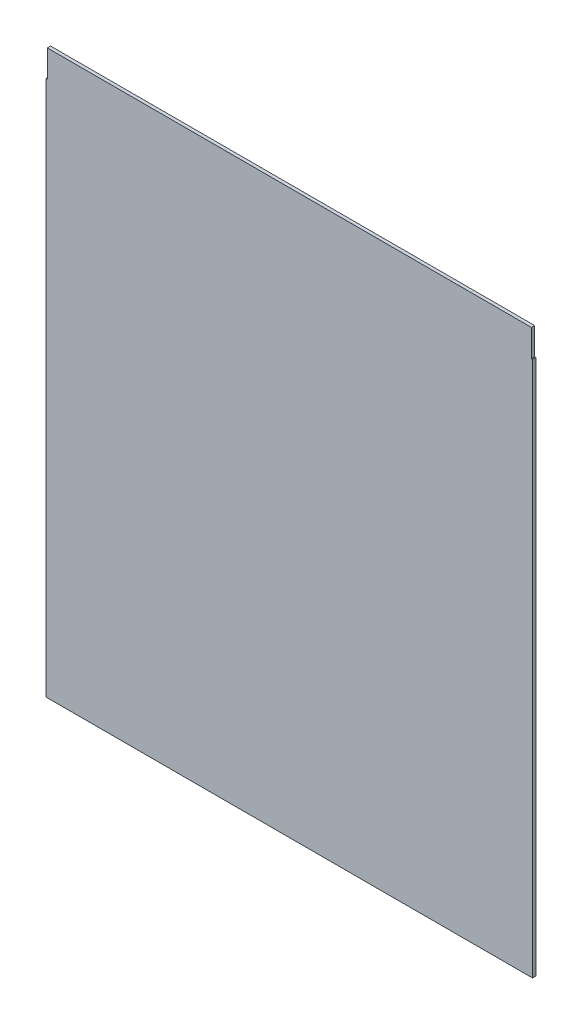
SolidWorks part; units mm, degrees
ref_plane "Alzado" through (0, 0, 0) normal (0, 0, 1) x (1, 0, 0)
ref_plane "Planta" through (0, 0, 0) normal (0, 1, 0) x (1, 0, 0)
ref_plane "Vista lateral" through (0, 0, 0) normal (1, 0, 0) x (0, 0, -1)
sketch "Croquis1" plane through (0, 0, 0) normal (0, 0, 1) x (1, 0, 0)
  line L0 (-261.8387, 298.7033) -> (-260.8387, 298.7033)
  line L1 (-260.8387, 323.7033) -> (187.1613, 323.7033)
  line L2 (-261.8387, 298.7033) -> (-261.8387, -197.0967)
  line L3 (-261.8387, -197.0967) -> (188.1613, -197.0967)
  line L4 (188.1613, 298.7033) -> (188.1613, -197.0967)
  line L5 (-260.8387, 298.7033) -> (-260.8387, 323.7033)
  line L6 (187.1613, 323.7033) -> (187.1613, 298.7033)
  line L7 (187.1613, 298.7033) -> (188.1613, 298.7033)
  dimension "D1" = 520.8
  dimension "D2" = 450
  dimension "D3" = 1
  dimension "D4" = 25
  dimension "D5" = 1
  dimension "D6" = 25
extrude "Saliente-Extruir1" add sketch "Croquis1" along normal blind 3
